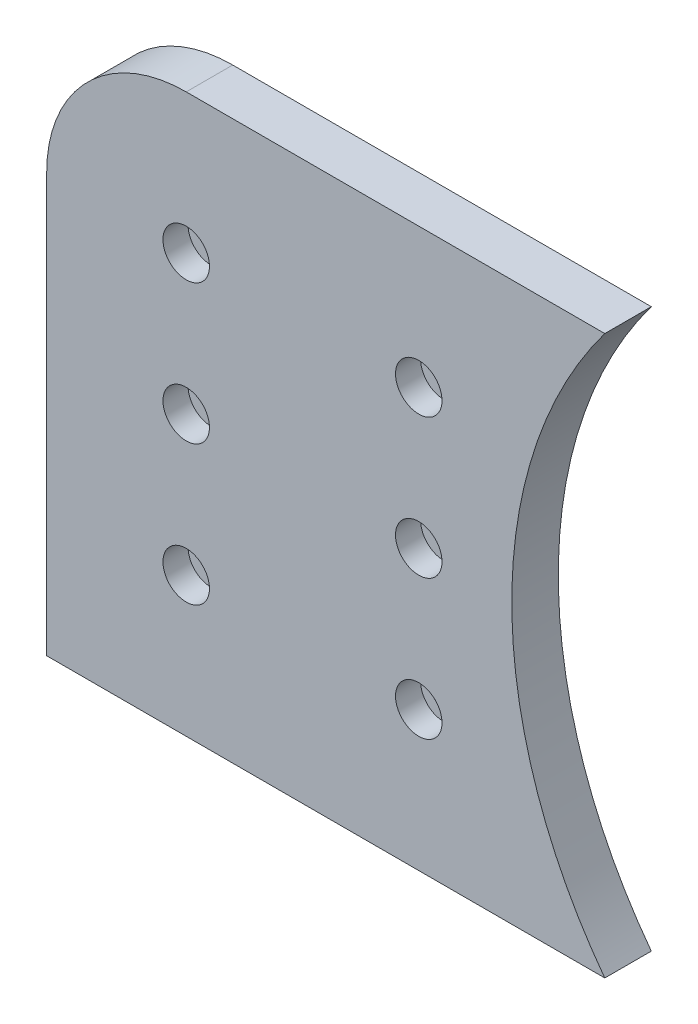
SolidWorks part; units mm, degrees
ref_plane "Vorne" through (0, 0, 0) normal (0, 0, 1) x (1, 0, 0)
ref_plane "Oben" through (0, 0, 0) normal (0, 1, 0) x (1, 0, 0)
ref_plane "Rechts" through (0, 0, 0) normal (1, 0, 0) x (0, 0, -1)
sketch "Skizze1" plane through (0, 0, 0) normal (0, 0, 1) x (1, 0, 0)
  line L1 (-120, 60) -> (0, 60)
  line L3 (-120, -60) -> (0, -60)
  line L4 (0, 60) -> (0, -60)
  arc A0 (-120, 60) -> (-120, -60) centre (-200, 0) cw
  dimension "D1" = 100
  dimension "D2" = 120
extrude "Aufsatz-Linear austragen1" add sketch "Skizze1" along normal mid plane 10
fillet "Verrundung1" radius 30 1 edges at (0, 60, 0)
hole_wizard "Stirnsenkung für M5 Zylinderschraube mit Innensechskant1" positions "Skizze5" profile "Skizze4" counterbore size "M5" standard "ISO" end condition through all
sketch "Skizze5" plane through (0, 0, 5) normal (0, 0, 1) x (1, 0, 0)
  arc A0 (0, 30) -> (-30, 60) centre (-30, 30) ccw construction
  point P0 (-30, 30)
sketch "Skizze4" plane through (-30, 30, 5) normal (1, 0, 0) x (0, -1, 0)
  line L0 (0, 0) -> (0, 10)
  line L1 (0, 10) -> (2.65, 10)
  line L3 (2.65, 10) -> (2.65, 5.4)
  line L4 (2.65, 5.4) -> (5, 5.4)
  line L5 (5, 5.4) -> (5, 0)
  line L7 (5, 0) -> (0, 0)
  line L11 (0, -6.35) -> (0, 107.95) construction
  dimension "Bohrerdurchmesser" = 5.3
  dimension "Bohrungstiefe" = 10
  dimension "Senkdurchmesser2" = 10
  dimension "Senktiefe2" = 5.4
pattern_linear "Lineares Muster1" count 3 spacing 30 along (0, -1, 0) count 2 spacing 50 along (-1, 0, 0) of "Stirnsenkung für M5 Zylinderschraube mit Innensechskant1"
mirror "Spiegeln1" about plane through (0, 60, 5) normal (-1, 0, 0) of bodies 103
delete or keep bodies "Körper-Löschen1" type delete bodies bodies 103
